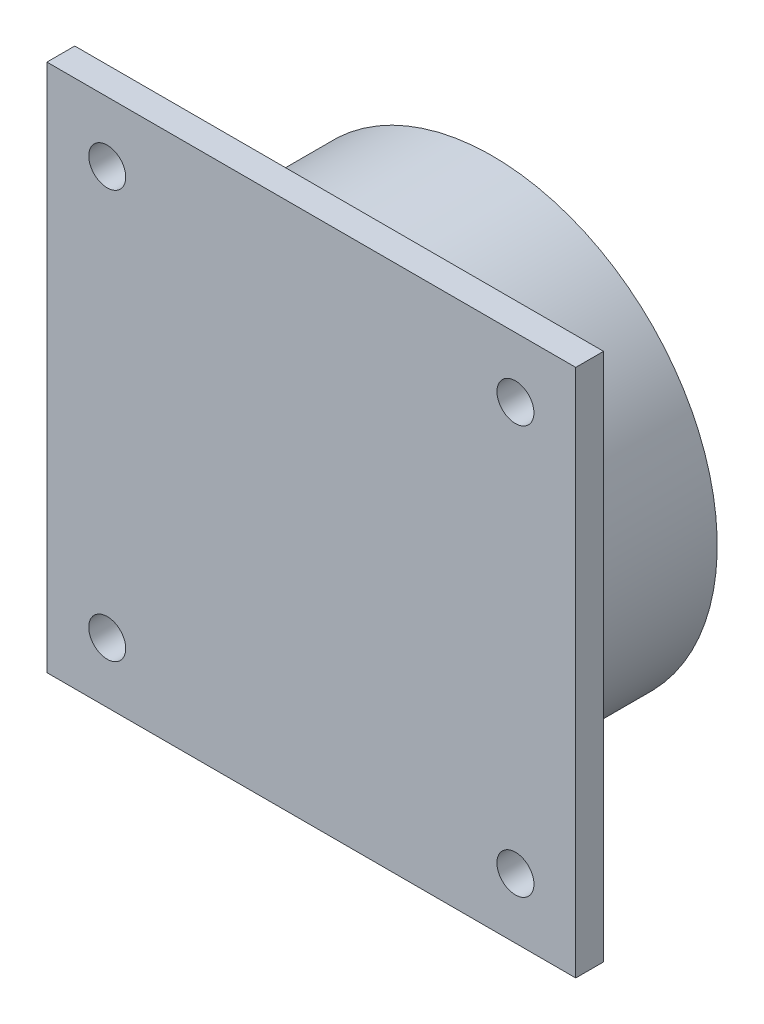
SolidWorks part; units mm, degrees
ref_plane "Front Plane" through (0, 0, 0) normal (0, 0, 1) x (1, 0, 0)
ref_plane "Top Plane" through (0, 0, 0) normal (0, 1, 0) x (1, 0, 0)
ref_plane "Right Plane" through (0, 0, 0) normal (1, 0, 0) x (0, 0, -1)
sketch "Sketch2" plane through (0, 0, 0) normal (0, 0, 1) x (1, 0, 0)
  line L1 (-13.908, 32.946) -> (43.092, 32.946)
  line L2 (-13.908, 32.946) -> (-13.908, -24.054)
  line L3 (-13.908, -24.054) -> (43.092, -24.054)
  line L4 (43.092, 32.946) -> (43.092, -24.054)
  dimension "D1" = 57
  dimension "D2" = 57
extrude "Boss-Extrude1" add sketch "Sketch2" along normal blind 3
sketch "Sketch3" plane through (0, 0, 0) normal (0, 0, -1) x (-1, 0, 0)
  line L0 (13.908, 4.446) -> (-43.092, 4.446) construction
  line L1 (13.908, 32.946) -> (13.908, -24.054) construction
  line L2 (-43.092, -24.054) -> (-43.092, 32.946) construction
  line L4 (-43.092, 32.946) -> (13.908, 32.946) construction
  line L5 (-14.592, 32.946) -> (-14.592, -24.054) construction
  line L6 (13.908, -24.054) -> (-43.092, -24.054) construction
  circle A0 centre (-14.592, 4.446) radius 24.25
  point P8 (0, 0)
  dimension "D1" = 48.5
extrude "Boss-Extrude2" add sketch "Sketch3" along normal blind 16.5
sketch "Sketch4" plane through (0, 0, 3) normal (0, 0, 1) x (1, 0, 0)
  line L0 (43.092, 4.446) -> (-13.908, 4.446) construction
  line L1 (43.092, -24.054) -> (43.092, 32.946) construction
  line L2 (-13.908, 32.946) -> (-13.908, -24.054) construction
  line L3 (36.592, 26.446) -> (36.592, -17.554) construction
  line L4 (43.092, 32.946) -> (-13.908, 32.946) construction
  line L5 (14.592, 32.946) -> (14.592, -24.054) construction
  line L6 (-13.908, -24.054) -> (43.092, -24.054) construction
  line L7 (36.592, -17.554) -> (-7.408, -17.554) construction
  circle A0 centre (36.592, 26.446) radius 1.9939
  circle A1 centre (36.592, -17.554) radius 1.9939
  circle A2 centre (-7.408, -17.554) radius 1.9939
  circle A3 centre (-7.408, 26.446) radius 1.9939
  point P8 (14.592, -17.554)
  point P15 (36.592, 4.446)
  dimension "D1" = 3.9878
  dimension "D2" = 44
  dimension "D3" = 44
extrude "Cut-Extrude1" cut sketch "Sketch4" against normal blind 16.5
